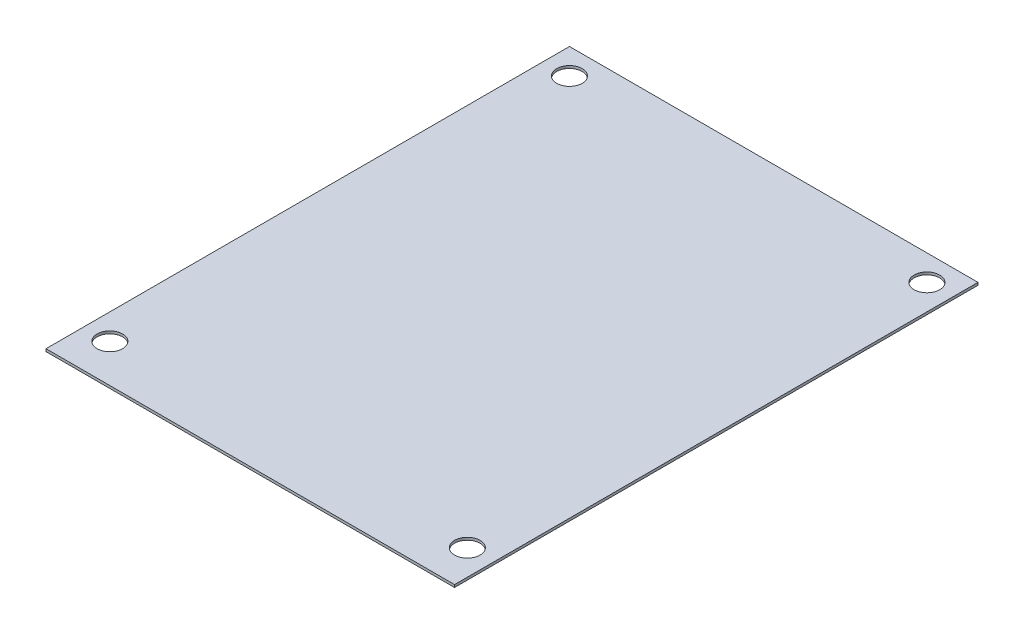
SolidWorks part; units mm, degrees
ref_plane "前视基准面" through (0, 0, 0) normal (0, 0, 1) x (1, 0, 0)
ref_plane "上视基准面" through (0, 0, 0) normal (0, 1, 0) x (1, 0, 0)
ref_plane "右视基准面" through (0, 0, 0) normal (1, 0, 0) x (0, 0, -1)
sketch "草图1" plane through (0, 0, 0) normal (0, 1, 0) x (1, 0, 0)
  line L1 (0, 0) -> (320, 0)
  line L2 (0, 0) -> (0, 410)
  line L3 (0, 410) -> (320, 410)
  line L4 (320, 0) -> (320, 410)
  dimension "D1" = 320
  dimension "D2" = 410
extrude "凸台-拉伸1" add sketch "草图1" along normal blind 2
sketch "草图2" plane through (0, 2, 0) normal (0, 1, 0) x (1, 0, 0)
  line L0 (320, 410) -> (0, 410) construction
  line L1 (20, 390) -> (300, 390) construction
  line L2 (20, 390) -> (20, 30) construction
  line L3 (20, 30) -> (300, 30) construction
  line L4 (300, 390) -> (300, 30) construction
  line L5 (320, 0) -> (320, 410) construction
  circle A0 centre (20, 390) radius 10
  circle A1 centre (300, 390) radius 10
  circle A2 centre (300, 30) radius 10
  circle A3 centre (20, 30) radius 10
  point P8 (26.8115, 21.6786)
  dimension "D1" = 20
  dimension "D2" = 280
  dimension "D3" = 360
  dimension "D4" = 20
  dimension "D5" = 20
extrude "切除-拉伸1" cut sketch "草图2" against normal blind 2
